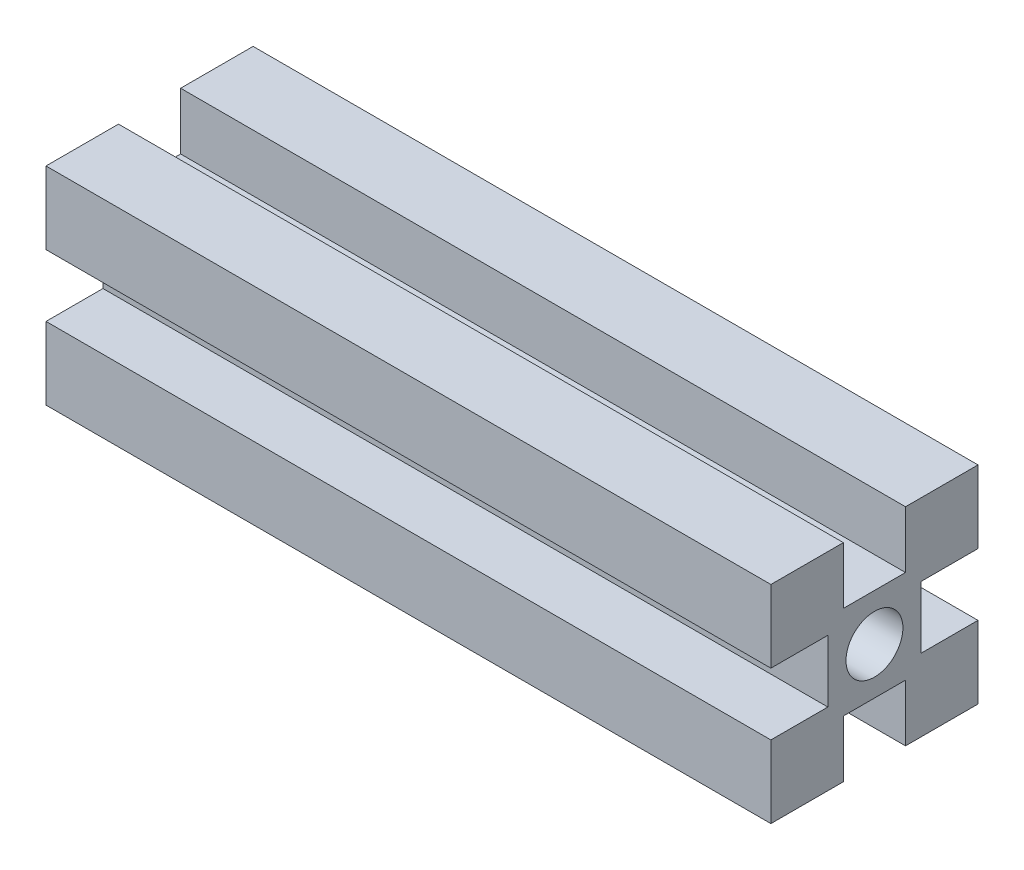
SolidWorks part; units mm, degrees
ref_plane "Plan de face" through (0, 0, 0) normal (0, 0, 1) x (1, 0, 0)
ref_plane "Plan de dessus" through (0, 0, 0) normal (0, 1, 0) x (1, 0, 0)
ref_plane "Plan de droite" through (0, 0, 0) normal (1, 0, 0) x (0, 0, -1)
ref_plane "Plan4" through (0, 0, 0) normal (-1, 0, 0) x (0, -1, 0)
sketch "Esquisse1" plane through (0, 0, 0) normal (-1, 0, 0) x (0, -1, 0)
  line L0 (-3, -10) -> (-3, -4.5)
  line L1 (-3, -4.5) -> (3, -4.5)
  line L2 (3, -4.5) -> (3, -10)
  line L3 (3, -10) -> (10, -10)
  line L4 (10, -10) -> (10, -3)
  line L5 (10, -3) -> (4.5, -3)
  line L6 (4.5, -3) -> (4.5, 3)
  line L7 (4.5, 3) -> (10, 3)
  line L8 (10, 3) -> (10, 10)
  line L9 (10, 10) -> (3, 10)
  line L10 (3, 10) -> (3, 4.5)
  line L11 (3, 4.5) -> (-3, 4.5)
  line L12 (-3, 4.5) -> (-3, 10)
  line L13 (-3, 10) -> (-10, 10)
  line L14 (-10, 10) -> (-10, 3)
  line L15 (-10, 3) -> (-4.5, 3)
  line L16 (-4.5, 3) -> (-4.5, -3)
  line L17 (-4.5, -3) -> (-10, -3)
  line L18 (-10, -3) -> (-10, -10)
  line L19 (-10, -10) -> (-3, -10)
  circle A0 centre (0, 0) radius 2.75
extrude "Boss.-Extru.1" add sketch "Esquisse1" against normal blind 70
